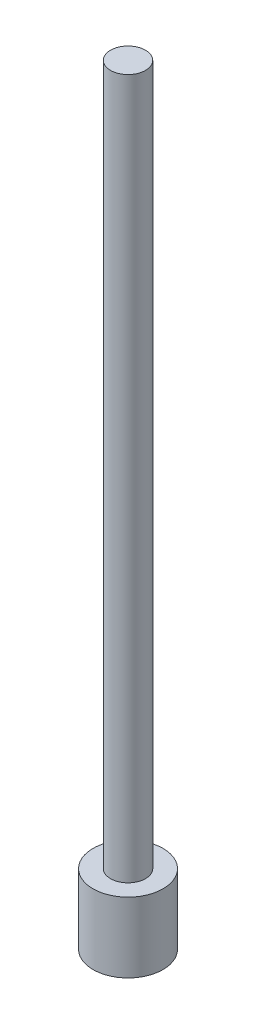
SolidWorks part; units mm, degrees
ref_plane "Front Plane" through (0, 0, 0) normal (0, 0, 1) x (1, 0, 0)
ref_plane "Top Plane" through (0, 0, 0) normal (0, 1, 0) x (1, 0, 0)
ref_plane "Right Plane" through (0, 0, 0) normal (1, 0, 0) x (0, 0, -1)
sketch "Sketch1" plane through (0, 0, 0) normal (0, 1, 0) x (1, 0, 0)
  circle A0 centre (0, 0) radius 0.25
  dimension "D1" = 0.5
extrude "Boss-Extrude1" add sketch "Sketch1" against normal blind 10
sketch "Sketch2" plane through (0, -10, 0) normal (0, -1, 0) x (1, 0, 0)
  circle A0 centre (0, 0) radius 0.5
  dimension "D1" = 1
extrude "Boss-Extrude2" add sketch "Sketch2" along normal blind 1
scale "Scale1" scale about origin uniform scaling yes scale factor 100
